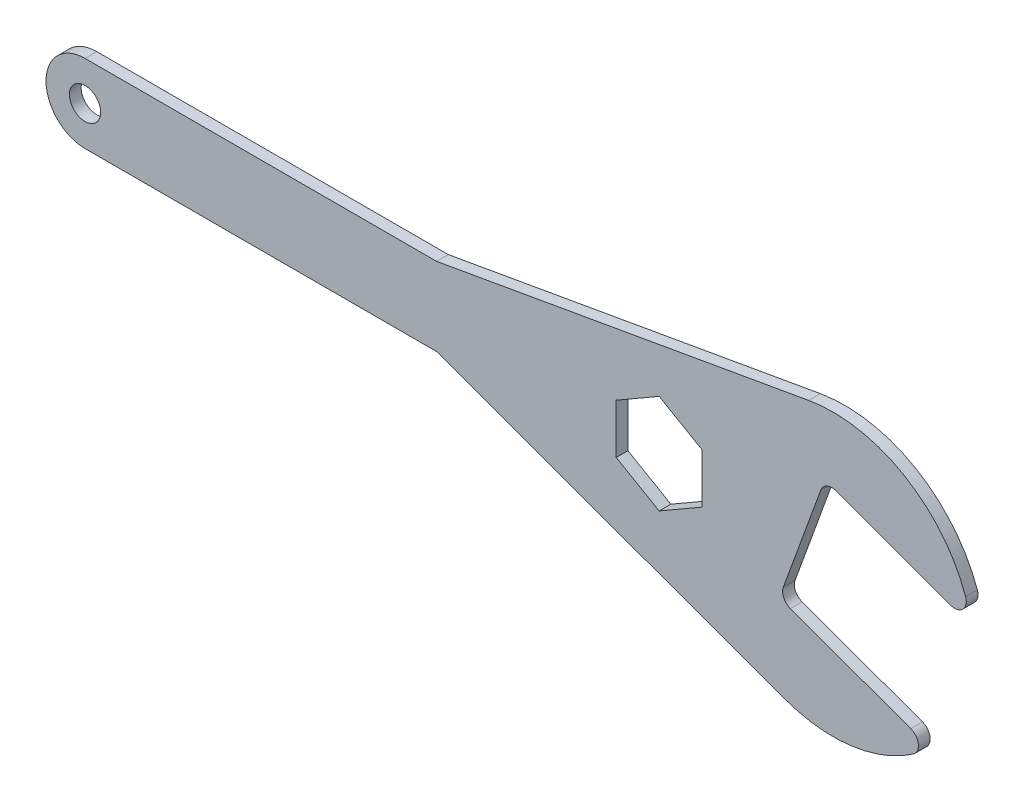
SolidWorks part; units mm, degrees
ref_plane "Front Plane" through (0, 0, 0) normal (0, 0, 1) x (1, 0, 0)
ref_plane "Top Plane" through (0, 0, 0) normal (0, 1, 0) x (1, 0, 0)
ref_plane "Right Plane" through (0, 0, 0) normal (1, 0, 0) x (0, 0, -1)
sketch "Sketch2" plane through (0, 0, 0) normal (0, 0, 1) x (1, 0, 0)
  line L0 (0, 10) -> (90, 10)
  line L1 (0, -10) -> (89.9805, -10)
  line L2 (90, 10) -> (185.2829, 26.8009)
  line L3 (89.9805, -10) -> (179.2215, -42.4811)
  line L4 (226.9873, -2.4008) -> (189.3996, 11.28)
  line L5 (189.3996, 11.28) -> (177.7709, -20.6695)
  line L6 (177.7709, -20.6695) -> (216.3661, -34.717)
  arc A0 (0, 10) -> (0, -10) centre (0, 0) ccw
  arc A1 (185.2829, 26.8009) -> (226.9873, -2.4008) centre (191.5342, -8.6521) cw
  arc A2 (179.2215, -42.4811) -> (216.3661, -34.717) centre (191.5342, -8.6521) ccw
  point P12 (179.2346, -19.8809)
  point P16 (179.2346, -17.9996)
  point P17 (175.4072, -29.2876)
  point P18 (179.2346, -32.2141)
  point P19 (177.7066, -29.7057)
  point P20 (0, 0)
  point P21 (0, 0)
  point P22 (0, 0)
  dimension "D1" = 20
  dimension "D5" = 36
  dimension "D2" = 100
  dimension "D3" = 170
  dimension "D4" = 34
  dimension "D6" = 227
  dimension "D7" = 160
  dimension "D8" = 40
  dimension "D9" = 20
extrude "Boss-Extrude1" add sketch "Sketch2" along normal blind 3
sketch "Sketch3" plane through (0, 0, 3) normal (0, 0, 1) x (1, 0, 0)
  line L1 (147, -16.8507) -> (158, -10.4998)
  line L2 (158, -10.4998) -> (158, 2.2019)
  line L3 (158, 2.2019) -> (147, 8.5527)
  line L4 (147, 8.5527) -> (136, 2.2019)
  line L5 (136, 2.2019) -> (136, -10.4998)
  line L6 (136, -10.4998) -> (147, -16.8507)
  line L7 (89.9805, -10) -> (179.2215, -42.4811) construction
  circle A0 centre (0, 0) radius 4
  circle A1 centre (147, -4.149) radius 11 construction
  arc A2 (0, 10) -> (0, -10) centre (0, 0) ccw construction
  point P4 (0, 0)
  point P14 (0, 0)
  point P15 (0, 0)
  point P19 (-10, 0)
  point P20 (0, 0)
  dimension "D1" = 8
  dimension "D2" = 22
  dimension "D3" = 25
  dimension "D4" = 146
extrude "Cut-Extrude1" cut sketch "Sketch3" against normal blind 3
fillet "Fillet2" radius 3 1 edges at (216.3661, -34.717, 1.5)
fillet "Fillet3" radius 3 1 edges at (226.9873, -2.4008, 1.5)
fillet "Fillet4" radius 3 1 edges at (177.7709, -20.6695, 1.5)
fillet "Fillet5" radius 3 1 edges at (189.3996, 11.28, 1.5)
